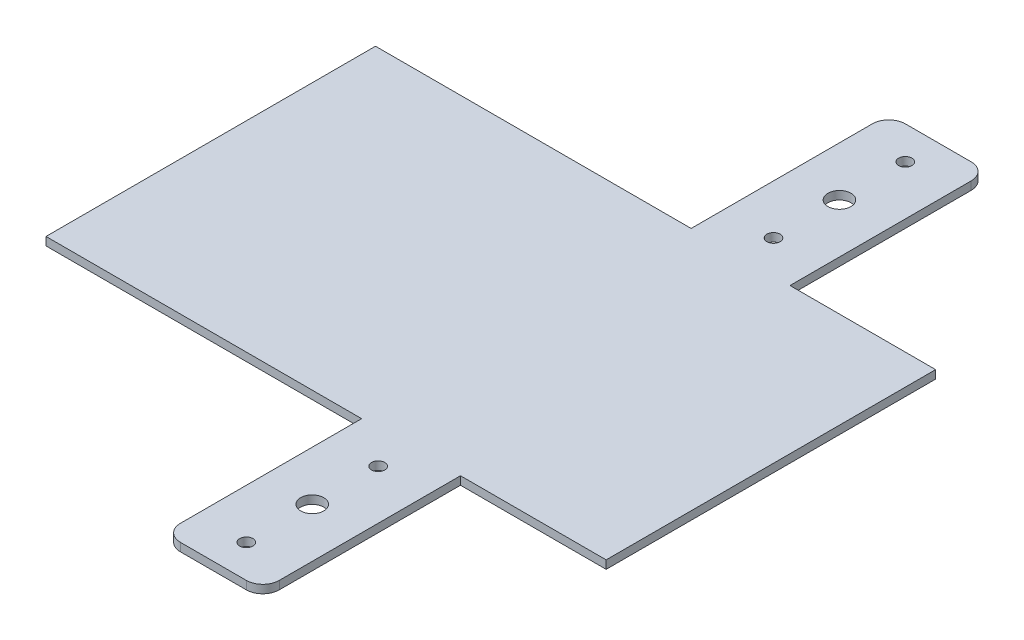
SolidWorks part; units mm, degrees
ref_plane "Front" through (0, 0, 0) normal (0, 0, 1) x (1, 0, 0)
ref_plane "Top" through (0, 0, 0) normal (0, 1, 0) x (1, 0, 0)
ref_plane "Right" through (0, 0, 0) normal (1, 0, 0) x (0, 0, -1)
sketch "Sketch1" plane through (0, 0, 0) normal (0, 1, 0) x (1, 0, 0)
  line L0 (-449.7086, 415.6316) -> (-361.2965, 415.6316)
  line L1 (-701.2965, 415.6316) -> (-509.7086, 415.6316)
  line L2 (-701.2965, 415.6316) -> (-701.2965, 215.6316)
  line L3 (-701.2965, 215.6316) -> (-509.7086, 215.6316)
  line L4 (-361.2965, 415.6316) -> (-361.2965, 215.6316)
  line L6 (-509.7086, 415.6316) -> (-509.7086, 525.6316)
  line L7 (-499.7086, 535.6316) -> (-459.7086, 535.6316)
  line L8 (-449.7086, 415.6316) -> (-449.7086, 525.6316)
  line L9 (-361.2965, 315.6316) -> (-701.2965, 315.6316) construction
  line L10 (-449.7086, 215.6316) -> (-449.7086, 105.6316)
  line L11 (-499.7086, 95.6316) -> (-459.7086, 95.6316)
  line L12 (-509.7086, 215.6316) -> (-509.7086, 105.6316)
  line L13 (-449.7086, 215.6316) -> (-361.2965, 215.6316)
  arc A0 (-459.7086, 535.6316) -> (-449.7086, 525.6316) centre (-459.7086, 525.6316) cw
  arc A1 (-509.7086, 525.6316) -> (-499.7086, 535.6316) centre (-499.7086, 525.6316) cw
  arc A2 (-509.7086, 105.6316) -> (-499.7086, 95.6316) centre (-499.7086, 105.6316) ccw
  arc A3 (-459.7086, 95.6316) -> (-449.7086, 105.6316) centre (-459.7086, 105.6316) ccw
  circle A4 centre (-479.7086, 475.6316) radius 7
  circle A5 centre (-479.7086, 155.6316) radius 7
  point P10 (-449.7086, 535.6316)
  point P13 (-509.7086, 535.6316)
  point P24 (-509.7086, 95.6316)
  point P25 (-449.7086, 95.6316)
  dimension "D5" = 10
  dimension "D6" = 320
  dimension "D8" = 118.4122
  dimension "D1" = 340
  dimension "D2" = 200
  dimension "D3" = 60
  dimension "D4" = 120
  dimension "D7" = 160
  dimension "D9" = 30
extrude "Boss-Extrude1" add sketch "Sketch1" along normal blind 5
sketch "Sketch2" plane through (0, 5, 0) normal (0, 1, 0) x (1, 0, 0)
  line L0 (-479.7086, 535.6316) -> (-479.7086, 95.6316) construction
  line L1 (-459.7086, 535.6316) -> (-499.7086, 535.6316) construction
  line L2 (-499.7086, 95.6316) -> (-459.7086, 95.6316) construction
  line L3 (-361.2965, 315.6316) -> (-701.2965, 315.6316) construction
  line L4 (-361.2965, 215.6316) -> (-361.2965, 415.6316) construction
  line L5 (-701.2965, 415.6316) -> (-701.2965, 215.6316) construction
  circle A0 centre (-479.7086, 195.6316) radius 4
  circle A1 centre (-479.7086, 115.6316) radius 4
  circle A2 centre (-479.7086, 155.6316) radius 7 construction
  circle A3 centre (-479.7086, 515.6316) radius 4
  circle A4 centre (-479.7086, 435.6316) radius 4
  dimension "D1" = 80
  dimension "D2" = 40
extrude "Cut-Extrude1" cut sketch "Sketch2" against normal through all
